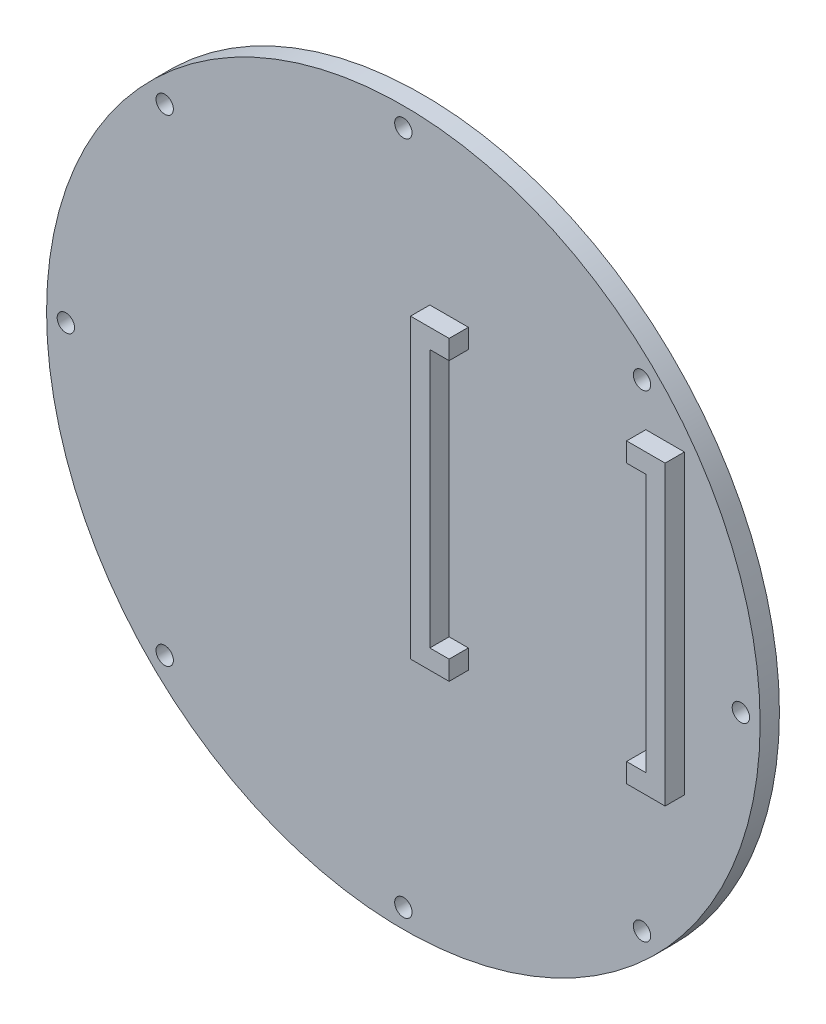
SolidWorks part; units mm, degrees
material "ABS"
ref_plane "Ön Düzlem" through (0, 0, 0) normal (0, 0, 1) x (1, 0, 0)
ref_plane "Üst Düzlem" through (0, 0, 0) normal (0, 1, 0) x (1, 0, 0)
ref_plane "Sağ Düzlem" through (0, 0, 0) normal (1, 0, 0) x (0, 0, -1)
sketch "Sketch1" plane through (0, 0, 0) normal (0, 0, 1) x (1, 0, 0)
  circle A0 centre (0, 0) radius 92.5
  circle A1 centre (87.5, 0) radius 2.25
  circle A2 centre (61.8718, -61.8718) radius 2.25
  circle A3 centre (0, -87.5) radius 2.25
  circle A4 centre (-61.8718, -61.8718) radius 2.25
  circle A5 centre (-87.5, 0) radius 2.25
  circle A6 centre (-61.8718, 61.8718) radius 2.25
  circle A7 centre (0, 87.5) radius 2.25
  circle A8 centre (61.8718, 61.8718) radius 2.25
  point P22 (0, 0)
  dimension "D1" = 185
  dimension "D2" = 87.5
extrude "Boss-Extrude1" add sketch "Sketch1" along normal blind 5 contours A0
sketch "Sketch12" plane through (0, 0, 5) normal (0, 0, 1) x (1, 0, 0)
  line L0 (62.8618, -20.8415) -> (67.8618, -20.8415)
  line L1 (11.8618, 46.1585) -> (11.8618, -20.8415)
  line L3 (11.8618, 46.1585) -> (16.8618, 46.1585)
  line L4 (16.8618, 46.1585) -> (16.8618, 51.1585)
  line L5 (16.8618, 51.1585) -> (6.8618, 51.1585)
  line L6 (6.8618, 51.1585) -> (6.8618, -25.8415)
  line L7 (6.8618, -25.8415) -> (16.8618, -25.8415)
  line L8 (16.8618, -25.8415) -> (16.8618, -20.8415)
  line L9 (16.8618, -20.8415) -> (11.8618, -20.8415)
  line L16 (39.8618, 16.7587) -> (39.8618, 55.2587) construction
  line L17 (62.8618, -25.8415) -> (62.8618, -20.8415)
  line L18 (72.8618, -25.8415) -> (62.8618, -25.8415)
  line L19 (72.8618, 51.1585) -> (72.8618, -25.8415)
  line L20 (62.8618, 51.1585) -> (72.8618, 51.1585)
  line L21 (62.8618, 46.1585) -> (62.8618, 51.1585)
  line L22 (67.8618, 46.1585) -> (62.8618, 46.1585)
  line L23 (67.8618, 46.1585) -> (67.8618, -20.8415)
  point P6 (11.8618, 12.6585)
  point P19 (67.8618, 12.6585)
  dimension "D1" = 67
  dimension "D2" = 77
  dimension "D3" = 10
  dimension "D4" = 5
  dimension "D5" = 5
extrude "Boss-Extrude2" add sketch "Sketch12" along normal blind 5
sketch "Sketch13" plane through (0, 0, 0) normal (0, 0, -1) x (-1, 0, 0)
  circle A0 centre (-87.5, 0) radius 2.25
  circle A1 centre (-61.8718, 61.8718) radius 2.25
  circle A2 centre (0, 87.5) radius 2.25
  circle A3 centre (61.8718, 61.8718) radius 2.25
  circle A4 centre (87.5, 0) radius 2.25
  circle A5 centre (61.8718, -61.8718) radius 2.25
  circle A6 centre (0, -87.5) radius 2.25
  circle A7 centre (-61.8718, -61.8718) radius 2.25
  point P19 (0, 0)
  dimension "D1" = 87.5
extrude "Cut-Extrude4" cut sketch "Sketch13" against normal up to next
